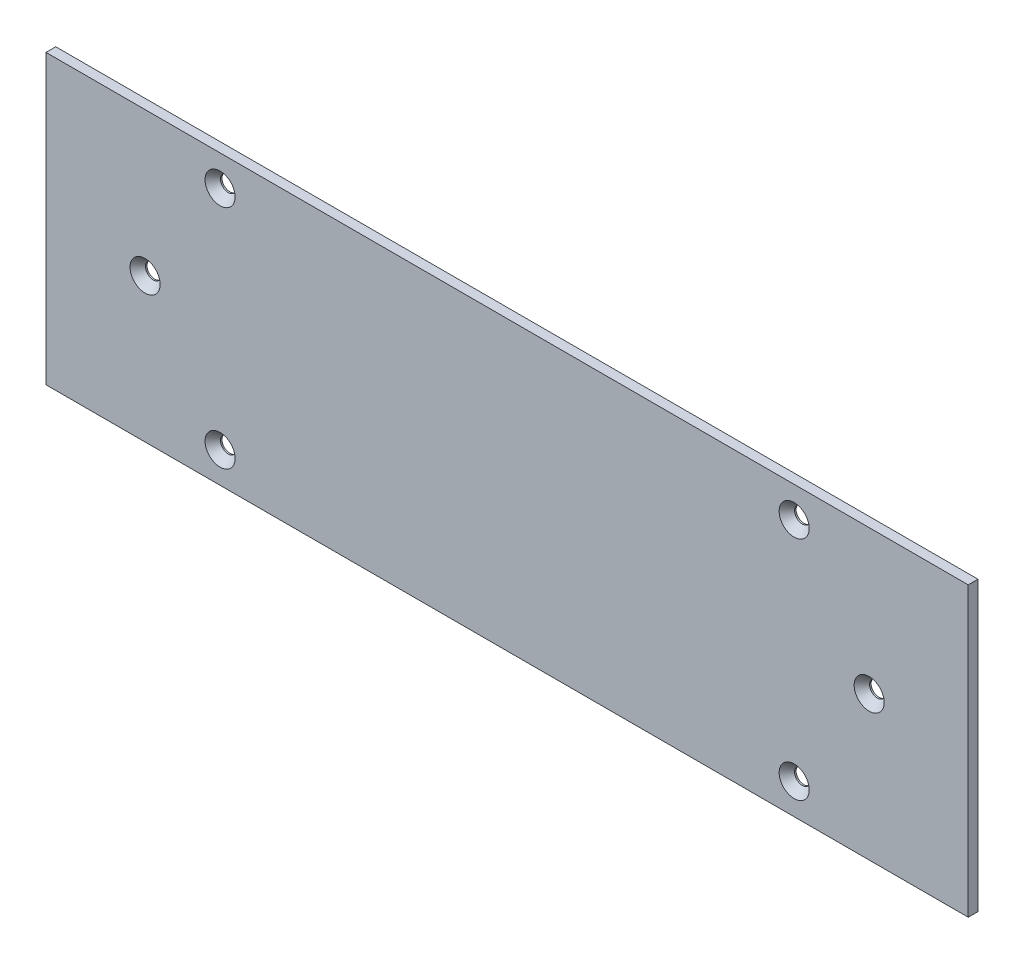
SolidWorks part; units mm, degrees
material "6061 Alloy"
ref_plane "Front Plane" through (0, 0, 0) normal (0, 0, 1) x (1, 0, 0)
ref_plane "Top Plane" through (0, 0, 0) normal (0, 1, 0) x (1, 0, 0)
ref_plane "Right Plane" through (0, 0, 0) normal (1, 0, 0) x (0, 0, -1)
sketch "Sketch1" plane through (0, 0, 0) normal (0, 0, 1) x (1, 0, 0)
  line L1 (-150, -46.825) -> (150, -46.825)
  line L2 (-150, -46.825) -> (-150, 46.825)
  line L3 (-150, 46.825) -> (150, 46.825)
  line L4 (150, -46.825) -> (150, 46.825)
  line L5 (-150, -46.825) -> (150, 46.825) construction
  line L6 (-150, 46.825) -> (150, -46.825) construction
  point P0 (0, 0)
  dimension "D1" = 300
  dimension "D2" = 93.65
extrude "Boss-Extrude1" add sketch "Sketch1" along normal blind 3.175
sketch "Sketch3" plane through (0, 0, 3.175) normal (0, 0, 1) x (1, 0, 0)
  point P0 (-93.375, 36.825)
  point P1 (93.375, 36.825)
  point P2 (93.375, -36.825)
  point P5 (-93.375, -36.825)
hole_wizard "CSK for #10 Flat Head Machine Screw1" positions "Sketch3" profile "Sketch4" countersink size "#10" standard "ANSI Inch"
sketch "Sketch4" plane through (-93.375, 36.825, 3.175) normal (1, 0, 0) x (0, -1, 0)
  line L0 (0, 0) -> (0, 6.3598)
  line L1 (0, 6.3598) -> (2.5527, 4.826)
  line L2 (2.5527, 4.826) -> (2.5527, 2.6882)
  line L3 (2.5527, 2.6882) -> (4.8895, 0)
  line L5 (4.8895, 0) -> (0, 0)
  line L6 (-2.5527, 2.6882) -> (-4.8895, 0) construction
  line L10 (0, 6.3598) -> (-2.5527, 4.826) construction
  line L11 (0, -6.35) -> (0, 107.95) construction
  dimension "Hole Dia." = 5.1054
  dimension "Hole Depth" = 4.826
  dimension "Near C'Sink Dia." = 9.779
  dimension "Near C'Sink Angle" = 82
  dimension "Drill Angle" = 118
sketch "Sketch5" plane through (0, 0, 3.175) normal (0, 0, 1) x (1, 0, 0)
  point P0 (-117.775, 0)
  point P1 (117.775, 0)
hole_wizard "CSK for #10 Flat Head Machine Screw2" positions "Sketch5" profile "Sketch6" countersink size "#10" standard "ANSI Inch"
sketch "Sketch6" plane through (-117.775, 0, 3.175) normal (1, 0, 0) x (0, -1, 0)
  line L0 (0, 0) -> (0, 6.3598)
  line L1 (0, 6.3598) -> (2.5527, 4.826)
  line L2 (2.5527, 4.826) -> (2.5527, 2.6882)
  line L3 (2.5527, 2.6882) -> (4.8895, 0)
  line L5 (4.8895, 0) -> (0, 0)
  line L6 (-2.5527, 2.6882) -> (-4.8895, 0) construction
  line L10 (0, 6.3598) -> (-2.5527, 4.826) construction
  line L11 (0, -6.35) -> (0, 107.95) construction
  dimension "Hole Dia." = 5.1054
  dimension "Hole Depth" = 4.826
  dimension "Near C'Sink Dia." = 9.779
  dimension "Near C'Sink Angle" = 82
  dimension "Drill Angle" = 118
equation "\"side\"= 100mm"
equation "\"thk\"= 1 / 8"
equation "\"D1@Sketch1\"=\"side\"*3"
equation "\"D2@Sketch1\"=\"side\"-(2*\"thk\")"
equation "\"D1@Boss-Extrude1\"=\"thk\""
